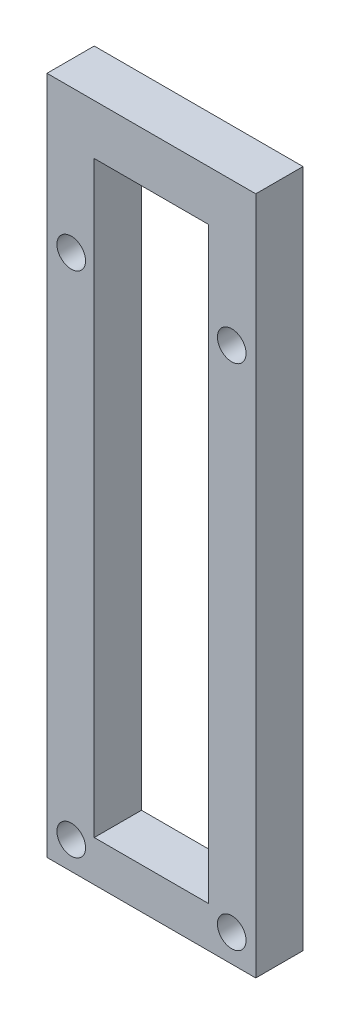
SolidWorks part; units mm, degrees
ref_plane "Front Plane" through (0, 0, 0) normal (0, 0, 1) x (1, 0, 0)
ref_plane "Top Plane" through (0, 0, 0) normal (0, 1, 0) x (1, 0, 0)
ref_plane "Right Plane" through (0, 0, 0) normal (1, 0, 0) x (0, 0, -1)
sketch "Sketch2" plane through (0, 0, 0) normal (0, 0, 1) x (1, 0, 0)
  line L0 (0, 0) -> (0, 94.86)
  line L1 (0, 94.86) -> (-6.6, 94.86)
  line L2 (-6.6, 94.86) -> (-6.6, 5.71)
  line L3 (-6.6, 5.71) -> (-22.56, 5.71)
  line L4 (-22.56, 5.71) -> (-22.56, 94.86)
  line L5 (-22.56, 94.86) -> (-29.16, 94.86)
  line L6 (-29.16, 94.86) -> (-29.16, 0)
  line L7 (-29.16, 0) -> (0, 0)
extrude "Boss-Extrude1" add sketch "Sketch2" along normal blind 6.6
sketch "Sketch3" plane through (-22.56, 0, 0) normal (1, 0, 0) x (0, 0, -1)
  line L0 (0, 5.71) -> (0, 94.86) construction
  line L1 (-6.6, 94.86) -> (0, 94.86)
  line L2 (-6.6, 94.86) -> (-6.6, 87.8561)
  line L3 (-6.6, 87.8561) -> (0, 87.8561)
  line L4 (0, 94.86) -> (0, 87.8561)
extrude "Boss-Extrude2" add sketch "Sketch3" along normal up to next
sketch "Sketch4" plane through (0, 0, 6.6) normal (0, 0, 1) x (1, 0, 0)
  line L0 (0, 94.86) -> (-29.16, 94.86) construction
  circle A0 centre (-3.3544, 47.4281) radius 2
  circle A1 centre (-25.771, 47.4281) radius 2
  circle A2 centre (-25.771, 3.86) radius 2
  circle A3 centre (-3.3544, 3.86) radius 2
  circle A4 centre (-25.771, 74.86) radius 2
  circle A5 centre (-3.3544, 74.86) radius 2
  dimension "D1" = 20
  dimension "D2" = 20
  dimension "D3" = 91
  dimension "D4" = 91
extrude "Cut-Extrude1" cut sketch "Sketch4" against normal blind 15
sketch "Sketch5" plane through (0, 0, 6.6) normal (0, 0, 1) x (1, 0, 0)
  circle A0 centre (-25.771, 47.4281) radius 2
  circle A1 centre (-3.3544, 47.4281) radius 2
extrude "Boss-Extrude3" add sketch "Sketch5" against normal blind 6.69
